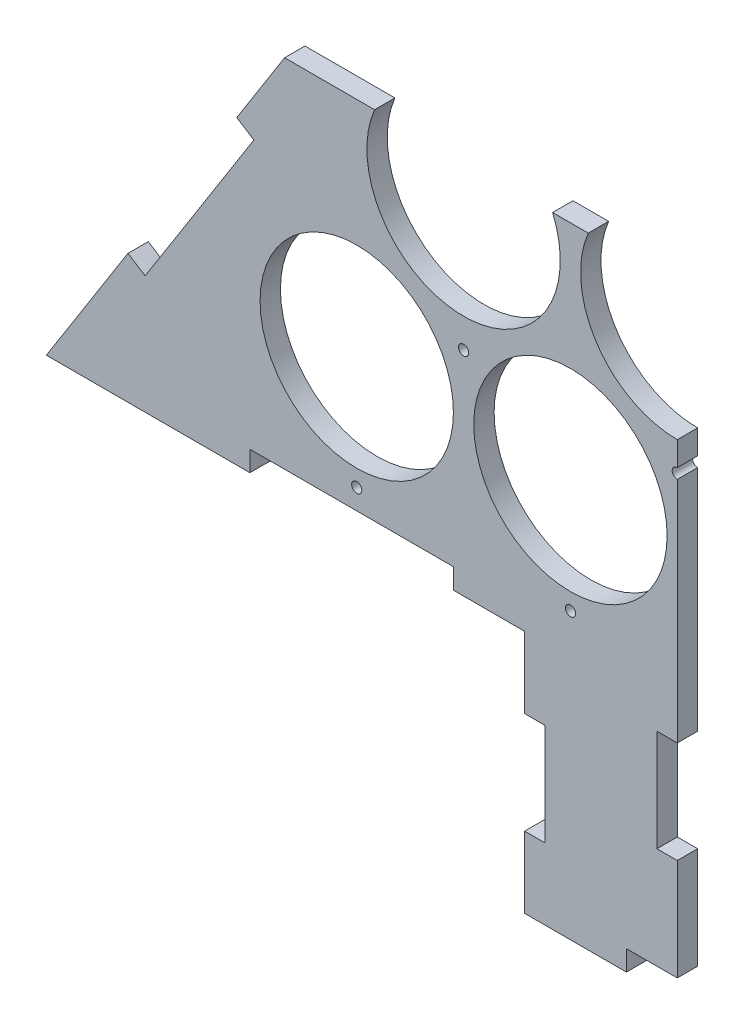
SolidWorks part; units mm, degrees
ref_plane "Plan de face" through (0, 0, 0) normal (0, 0, 1) x (1, 0, 0)
ref_plane "Plan de dessus" through (0, 0, 0) normal (0, 1, 0) x (1, 0, 0)
ref_plane "Plan de droite" through (0, 0, 0) normal (1, 0, 0) x (0, 0, -1)
sketch "Esquisse1" plane through (0, 0, 0) normal (0, 0, 1) x (1, 0, 0)
  line L0 (0, 0) -> (-371.1464, 0) construction
  line L1 (0, 0) -> (478.5179, 0) construction
  line L2 (0, 0) -> (0, 90.9327) construction
  line L3 (0, 90.9327) -> (-157.5, 90.9327) construction
  line L4 (0, 90.9327) -> (157.5, 90.9327) construction
  line L5 (0, 90.9327) -> (0, 181.8653) construction
  line L6 (0, 181.8653) -> (-52.5, 181.8653) construction
  line L7 (0, 181.8653) -> (52.5, 181.8653) construction
  line L8 (0, 181.8653) -> (0, 363.4062) construction
  line L9 (-310, -75.6429) -> (0, 414.5612)
  line L10 (0, 414.5612) -> (310, -75.6429)
  line L11 (310, -75.6429) -> (-310, -75.6429)
  circle A0 centre (-157.5, 0) radius 47.5
  circle A1 centre (-52.5, 0) radius 47.5
  circle A2 centre (52.5, 0) radius 47.5
  circle A3 centre (157.5, 0) radius 47.5
  circle A4 centre (-105, 90.9327) radius 47.5
  circle A5 centre (0, 90.9327) radius 47.5
  circle A6 centre (105, 90.9327) radius 47.5
  circle A7 centre (-52.5, 181.8653) radius 47.5
  circle A8 centre (52.5, 181.8653) radius 47.5
  circle A9 centre (0, 272.798) radius 47.5
  dimension "D1" = 95
  dimension "D2" = 95
  dimension "D3" = 95
  dimension "D4" = 95
  dimension "D5" = 105
  dimension "D6" = 52.5
  dimension "D7" = 52.5
  dimension "D8" = 105
  dimension "D9" = 95
  dimension "D10" = 95
  dimension "D11" = 95
  dimension "D12" = 105
  dimension "D13" = 105
  dimension "D14" = 105
  dimension "D15" = 95
  dimension "D16" = 95
  dimension "D17" = 105
  dimension "D18" = 52.5
  dimension "D19" = 52.5
  dimension "D20" = 95
  dimension "D21" = 105
  dimension "D22" = 80
  dimension "D23" = 620
  dimension "D24" = 580
  dimension "D25" = 0
  dimension "D26" = 580
extrude "Boss.-Extru.1" add sketch "Esquisse1" along normal blind 10
sketch "Esquisse3" plane through (0, 0, 10) normal (0, 0, 1) x (1, 0, 0)
  line L10 (-269.9138, -12.2544) -> (-261.462, -17.5992)
  line L15 (0, 414.5612) -> (-310, -75.6429) construction
  line L16 (-261.462, -17.5992) -> (-208.0137, 66.9187)
  line L17 (-208.0137, 66.9187) -> (-216.4655, 72.2635)
  line L18 (-216.4655, 72.2635) -> (-269.9138, -12.2544)
  line L19 (-181.7241, 127.2002) -> (-173.2723, 121.8554)
  line L20 (-173.2723, 121.8554) -> (-119.8241, 206.3733)
  line L21 (-119.8241, 206.3733) -> (-128.2759, 211.7181)
  line L22 (-128.2759, 211.7181) -> (-181.7241, 127.2002)
  line L23 (-93.5345, 266.6548) -> (-85.0827, 261.31)
  line L24 (-85.0827, 261.31) -> (-31.6344, 345.8279)
  line L25 (-31.6344, 345.8279) -> (-40.0862, 351.1727)
  line L26 (-40.0862, 351.1727) -> (-93.5345, 266.6548)
  line L27 (269.9138, -12.2544) -> (261.462, -17.5992)
  line L28 (310, -75.6429) -> (0, 414.5612) construction
  line L29 (261.462, -17.5992) -> (208.0137, 66.9187)
  line L30 (208.0137, 66.9187) -> (216.4655, 72.2635)
  line L31 (216.4655, 72.2635) -> (269.9138, -12.2544)
  line L32 (181.7241, 127.2002) -> (173.2723, 121.8554)
  line L33 (173.2723, 121.8554) -> (119.8241, 206.3733)
  line L34 (119.8241, 206.3733) -> (128.2759, 211.7181)
  line L35 (128.2759, 211.7181) -> (181.7241, 127.2002)
  line L36 (93.5345, 266.6548) -> (85.0827, 261.31)
  line L37 (85.0827, 261.31) -> (31.6344, 345.8279)
  line L38 (31.6344, 345.8279) -> (40.0862, 351.1727)
  line L39 (40.0862, 351.1727) -> (93.5345, 266.6548)
  line L40 (-310, -75.6429) -> (310, -75.6429) construction
  line L41 (-210, -75.6429) -> (-110, -75.6429)
  line L42 (-210, -75.6429) -> (-210, -65.6429)
  line L43 (-210, -65.6429) -> (-110, -65.6429)
  line L44 (-110, -75.6429) -> (-110, -65.6429)
  line L45 (0, 0) -> (0, -75.6429) construction
  line L46 (210, -65.6429) -> (110, -65.6429)
  line L47 (110, -75.6429) -> (110, -65.6429)
  line L48 (210, -75.6429) -> (110, -75.6429)
  line L49 (210, -75.6429) -> (210, -65.6429)
  dimension "D3" = 100
  dimension "D4" = 10
  dimension "D5" = 100
  dimension "D10" = 10
  dimension "D11" = 100
  dimension "D12" = 10
  dimension "D13" = 100
  dimension "D14" = 10
  dimension "D15" = 100
  dimension "D16" = 75
  dimension "D17" = 75
  dimension "D18" = 65
  dimension "D19" = 100
  dimension "D20" = 10
  dimension "D21" = 10
  dimension "D22" = 100
  dimension "D23" = 75
  dimension "D24" = 65
  dimension "D25" = 100
  dimension "D26" = 10
  dimension "D27" = 75
extrude "Enlèv. mat.-Extru.1" cut sketch "Esquisse3" against normal through all
sketch "Esquisse4" plane through (0, 0, 10) normal (0, 0, 1) x (1, 0, 0)
  line L0 (-110, -65.6429) -> (-210, -65.6429) construction
  circle A0 centre (-157.5, -55.6429) radius 2.5
  circle A3 centre (-52.5, -55.6429) radius 2.5
  circle A4 centre (52.5, -55.6429) radius 2.5
  circle A5 centre (157.5, -55.6429) radius 2.5
  circle A6 centre (-105, 29.0474) radius 2.5
  circle A8 centre (-157.5, 0) radius 47.5 construction
  circle A10 centre (-52.5, 0) radius 47.5 construction
  circle A12 centre (0, 29.0474) radius 2.5
  circle A13 centre (105, 29.0474) radius 2.5
  circle A14 centre (-52.5, 119.98) radius 2.5
  circle A15 centre (-105, 90.9327) radius 47.5 construction
  circle A16 centre (0, 90.9327) radius 47.5 construction
  circle A17 centre (52.5, 119.98) radius 2.5
  circle A18 centre (0, 210.9127) radius 2.5
  circle A19 centre (52.5, 181.8653) radius 47.5 construction
  circle A20 centre (-52.5, 181.8653) radius 47.5 construction
  dimension "D1" = 5
  dimension "D2" = 10
  dimension "D3" = 4
  dimension "D4" = 5
  dimension "D5" = 60
  dimension "D6" = 60
  dimension "D7" = 3
  dimension "D8" = 5
  dimension "D9" = 60
  dimension "D10" = 60
  dimension "D12" = 5
  dimension "D13" = 60
  dimension "D14" = 60
  dimension "D11" = 2
extrude "Enlèv. mat.-Extru.2" cut sketch "Esquisse4" against normal through all
sketch "Esquisse6" plane through (0, 0, 10) normal (0, 0, 1) x (1, 0, 0)
  line L0 (-110, -75.6429) -> (110, -75.6429) construction
  line L1 (-75, -75.6429) -> (75, -75.6429)
  line L2 (-75, -75.6429) -> (-75, -195.6429)
  line L3 (-75, -195.6429) -> (75, -195.6429)
  line L4 (75, -75.6429) -> (75, -195.6429)
  dimension "D1" = 150
  dimension "D2" = 120
  dimension "D3" = 75
extrude "Boss.-Extru.2" add sketch "Esquisse6" against normal blind 10
sketch "Esquisse7" plane through (0, 0, 10) normal (0, 0, 1) x (1, 0, 0)
  line L0 (-75, -75.6429) -> (-75, -195.6429) construction
  line L1 (-75, -110.6429) -> (-65, -110.6429)
  line L2 (-75, -110.6429) -> (-75, -160.6429)
  line L3 (-75, -160.6429) -> (-65, -160.6429)
  line L4 (-65, -110.6429) -> (-65, -160.6429)
  line L5 (-75, -195.6429) -> (75, -195.6429) construction
  line L6 (-25, -195.6429) -> (25, -195.6429)
  line L7 (-25, -195.6429) -> (-25, -185.6429)
  line L8 (-25, -185.6429) -> (25, -185.6429)
  line L9 (25, -195.6429) -> (25, -185.6429)
  line L10 (75, -195.6429) -> (75, -75.6429) construction
  line L11 (75, -160.6429) -> (65, -160.6429)
  line L12 (75, -160.6429) -> (75, -110.6429)
  line L13 (75, -110.6429) -> (65, -110.6429)
  line L14 (65, -160.6429) -> (65, -110.6429)
  line L15 (75, -75.6429) -> (110, -75.6429) construction
  line L16 (-110, -75.6429) -> (-75, -75.6429) construction
  dimension "D1" = 10
  dimension "D2" = 10
  dimension "D3" = 50
  dimension "D4" = 50
  dimension "D5" = 35
  dimension "D6" = 35
  dimension "D7" = 50
  dimension "D8" = 50
  dimension "D9" = 10
extrude "Enlèv. mat.-Extru.3" cut sketch "Esquisse7" against normal blind 10
sketch "Esquisse9" plane through (0, 0, 10) normal (0, 0, 1) x (1, 0, 0)
  line L1 (0, 414.5612) -> (316.2482, 414.5612)
  line L2 (0, 414.5612) -> (0, -195.6429)
  line L3 (0, -195.6429) -> (316.2482, -195.6429)
  line L4 (316.2482, 414.5612) -> (316.2482, -195.6429)
extrude "Enlèv. mat.-Extru.4" cut sketch "Esquisse9" against normal blind 10
sketch "Esquisse10" plane through (0, 0, 10) normal (0, 0, 1) x (1, 0, 0)
  line L0 (0, 414.5612) -> (0, 109.4612) construction
  line L3 (0, 109.4612) -> (-334.8982, 109.4612)
  line L4 (0, 109.4612) -> (0, 423.4707)
  line L5 (0, 423.4707) -> (-334.8982, 423.4707)
  line L6 (-334.8982, 109.4612) -> (-334.8982, 423.4707)
  dimension "D1" = 305.1
extrude "Enlèv. mat.-Extru.6" cut sketch "Esquisse10" against normal blind 10
sketch "Esquisse11" plane through (0, 0, 10) normal (0, 0, 1) x (1, 0, 0)
  line L0 (0, 26.5474) -> (0, -185.6429) construction
  line L1 (0, -135.6429) -> (-10, -135.6429)
  line L2 (0, -135.6429) -> (0, -85.6429)
  line L3 (0, -85.6429) -> (-10, -85.6429)
  line L4 (-10, -135.6429) -> (-10, -85.6429)
  line L6 (0, -185.6429) -> (-25, -185.6429) construction
  dimension "D1" = 50
  dimension "D2" = 50
  dimension "D3" = 10
extrude "Enlèv. mat.-Extru.7" cut sketch "Esquisse11" against normal blind 10
